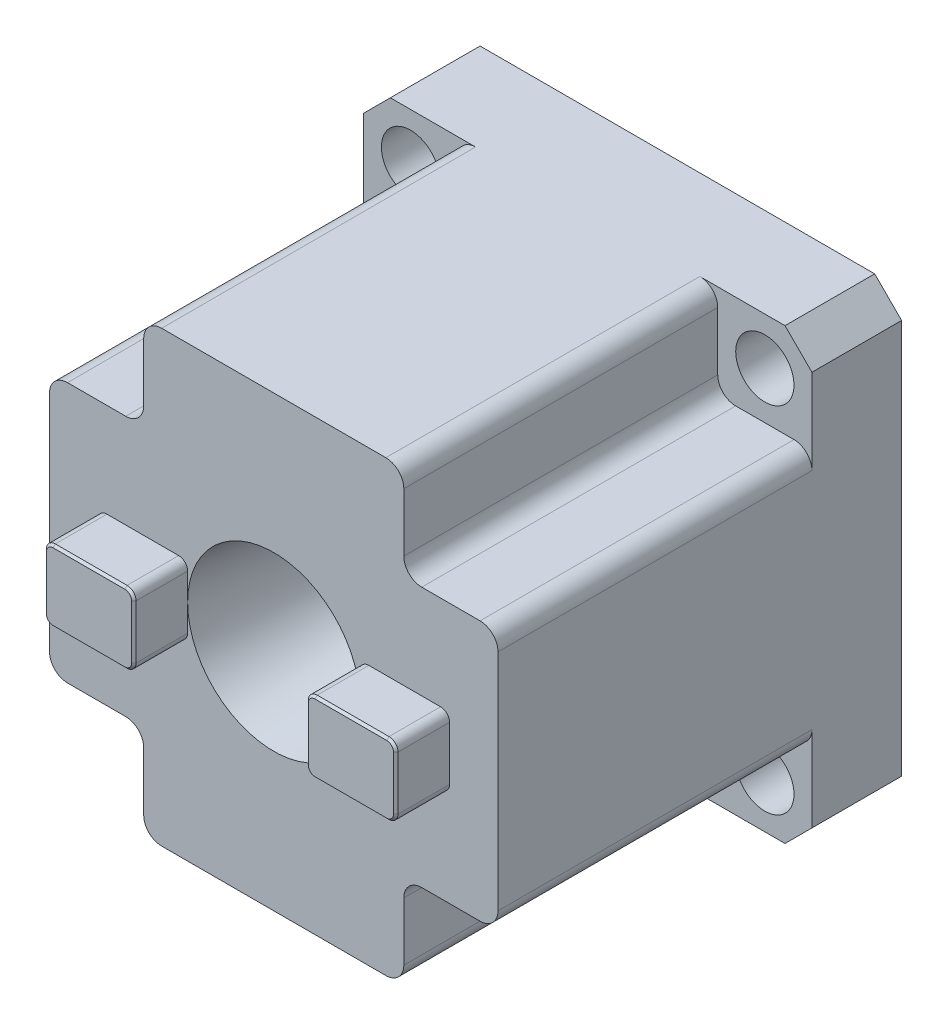
SolidWorks part; units mm, degrees
material "1.7147 (20MnCr5)"
ref_plane "前视基准面" through (0, 0, 0) normal (0, 0, 1) x (1, 0, 0)
ref_plane "上视基准面" through (0, 0, 0) normal (0, 1, 0) x (1, 0, 0)
ref_plane "右视基准面" through (0, 0, 0) normal (1, 0, 0) x (0, 0, -1)
other "Configuration Table"
sketch "草图1" plane through (0, 0, 0) normal (0, 0, 1) x (1, 0, 0)
  line L1 (0, 0) -> (50, 0)
  line L2 (0, 0) -> (0, -50)
  line L3 (0, -50) -> (50, -50)
  line L4 (50, 0) -> (50, -50)
  dimension "D1" = 50
  dimension "D2" = 50
extrude "凸台-拉伸1" add sketch "草图1" along normal blind 45
sketch "草图4" plane through (0, 0, 45) normal (0, 0, 1) x (1, 0, 0)
  line L0 (25, 0) -> (25, -50) construction
  line L1 (0, 0) -> (10.5, 0)
  line L2 (0, 0) -> (0, -10.5)
  line L3 (0, -10.5) -> (10.5, -10.5)
  line L4 (10.5, 0) -> (10.5, -10.5)
  line L5 (50, 0) -> (0, 0) construction
  line L6 (0, -50) -> (50, -50) construction
  line L7 (50, -25) -> (0, -25) construction
  line L8 (50, -50) -> (50, 0) construction
  line L9 (0, 0) -> (0, -50) construction
  line L10 (50, -10.5) -> (39.5, -10.5)
  line L11 (39.5, 0) -> (39.5, -10.5)
  line L12 (50, 0) -> (39.5, 0)
  line L13 (50, 0) -> (50, -10.5)
  line L14 (50, -50) -> (50, -39.5)
  line L15 (50, -50) -> (39.5, -50)
  line L16 (39.5, -50) -> (39.5, -39.5)
  line L17 (50, -39.5) -> (39.5, -39.5)
  line L18 (0, -39.5) -> (10.5, -39.5)
  line L19 (10.5, -50) -> (10.5, -39.5)
  line L20 (0, -50) -> (10.5, -50)
  line L21 (0, -50) -> (0, -39.5)
  dimension "D1" = 10.5
  dimension "D2" = 10.5
extrude "切除-拉伸1" cut sketch "草图4" against normal blind 35
fillet "圆角1" radius 2 12 edges at (0, -39.5, 27.5) (10.5, -39.5, 27.5) (10.5, -50, 27.5) (39.5, -50, 27.5) (39.5, -39.5, 27.5) (50, -39.5, 27.5) (50, -10.5, 27.5) (39.5, -10.5, 27.5) (39.5, 0, 27.5) (10.5, 0, 27.5) (10.5, -10.5, 27.5) (0, -10.5, 27.5)
chamfer "倒角1" distance 3 angle 45 4 edges at (50, -50, 5) (0, -50, 5) (0, 0, 5) (50, 0, 5)
sketch "草图5" plane through (0, 0, 10) normal (0, 0, 1) x (1, 0, 0)
  line L0 (0, -3) -> (0, -12.5) construction
  line L1 (12.5, 0) -> (3, 0) construction
  line L2 (25, 0) -> (25, -50) construction
  line L4 (37.5, 0) -> (12.5, 0) construction
  line L5 (12.5, -50) -> (37.5, -50) construction
  line L6 (0, -25) -> (50, -25) construction
  line L7 (0, -12.5) -> (0, -37.5) construction
  line L8 (50, -37.5) -> (50, -12.5) construction
  circle A0 centre (5.25, -5.25) radius 3.25
  circle A1 centre (44.75, -5.25) radius 3.25
  circle A2 centre (44.75, -44.75) radius 3.25
  circle A3 centre (5.25, -44.75) radius 3.25
  dimension "D3" = 6.5
  dimension "D1" = 5.25
  dimension "D2" = 5.25
extrude "切除-拉伸2" cut sketch "草图5" against normal through all
ref_plane "基准面1" through (25, 0, 0) normal (1, 0, 0) x (0, 0, -1)
sketch "草图6" plane through (25, 0, 0) normal (1, 0, 0) x (0, 0, -1)
  line L0 (0, -25) -> (-45, -25) construction
  line L1 (0, -47) -> (0, -3) construction
  line L2 (-45, -37.5) -> (-45, -12.5) construction
  line L3 (-45, -15.4) -> (-45, -25)
  line L4 (0, -25) -> (-45, -25)
  line L5 (-20.3143, -25) -> (-20.3143, -19) construction
  line L6 (-45, -15.4) -> (-20.3143, -19)
  line L7 (-20.3143, -19) -> (0, -19)
  line L10 (0, -19) -> (0, -25)
  dimension "D1" = 6
  dimension "D2" = 9.6
revolve "切除-旋转1" cut sketch "草图6" angle 360 about L0
sketch "草图7" plane through (0, 0, 45) normal (0, 0, 1) x (1, 0, 0)
  line L0 (0, -25) -> (50, -25) construction
  line L1 (0, -12.5) -> (0, -37.5) construction
  line L2 (50, -37.5) -> (50, -12.5) construction
  line L3 (34.6, -17.6463) -> (34.6, -32.8177) construction
  line L4 (25, -24.75) -> (25, 24.75) construction
  line L5 (34.6, -21) -> (44.6, -21)
  line L6 (34.6, -21) -> (34.6, -29)
  line L7 (34.6, -29) -> (44.6, -29)
  line L8 (44.6, -21) -> (44.6, -29)
  line L9 (15.4, -29) -> (5.4, -29)
  line L10 (5.4, -21) -> (5.4, -29)
  line L11 (15.4, -21) -> (5.4, -21)
  line L12 (15.4, -21) -> (15.4, -29)
  circle A0 centre (25, -25) radius 9.6 construction
  circle A1 centre (25, -25) radius 9.6 construction
  dimension "D1" = 10
  dimension "D2" = 8
  dimension "D3" = 4
extrude "凸台-拉伸4" add sketch "草图7" along normal blind 6
fillet "圆角2" radius 1 8 edges at (5.4, -21, 48) (5.4, -29, 48) (15.4, -29, 48) (15.4, -21, 48) (34.6, -21, 48) (44.6, -21, 48) (34.6, -29, 48) (44.6, -29, 48)
chamfer "倒角2" distance 0.25 angle 45 16 edges at (44.3071, -21.2929, 51) (44.6, -25, 51) (44.3071, -28.7071, 51) (39.6, -29, 51) (34.8929, -28.7071, 51) (34.6, -25, 51) (34.8929, -21.2929, 51) (39.6, -21, 51) (15.1071, -21.2929, 51) (15.4, -25, 51) (15.1071, -28.7071, 51) (10.4, -29, 51) (5.6929, -28.7071, 51) (5.4, -25, 51) (5.6929, -21.2929, 51) (10.4, -21, 51)
